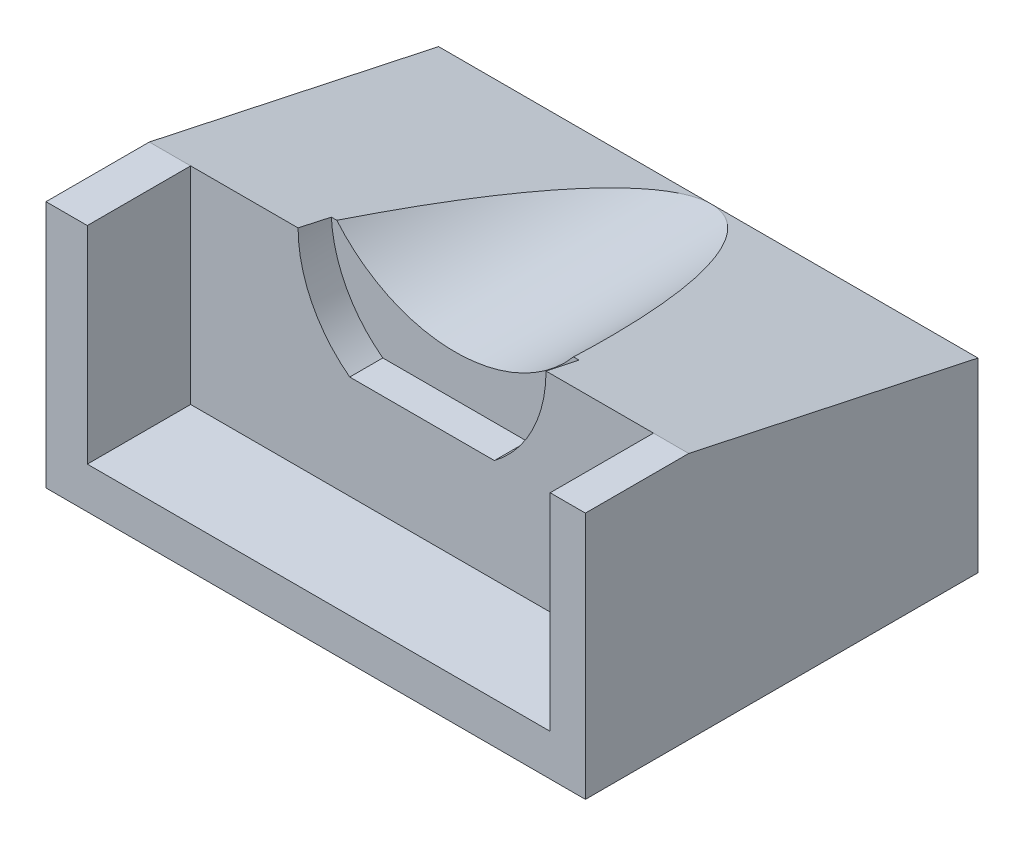
SolidWorks part; units mm, degrees
ref_plane "Front Plane" through (0, 0, 0) normal (0, 0, 1) x (1, 0, 0)
ref_plane "Top Plane" through (0, 0, 0) normal (0, 1, 0) x (1, 0, 0)
ref_plane "Right Plane" through (0, 0, 0) normal (1, 0, 0) x (0, 0, -1)
sketch "Sketch2" plane through (0, 0, 0) normal (0, 0, 1) x (1, 0, 0)
  line L1 (-11.2, 5) -> (11.2, 5)
  line L2 (-11.2, 5) -> (-11.2, -5)
  line L3 (-11.2, -5) -> (11.2, -5)
  line L4 (11.2, 5) -> (11.2, -5)
  line L5 (-11.2, 5) -> (11.2, -5) construction
  line L6 (-11.2, -5) -> (11.2, 5) construction
  point P0 (0, 0)
  dimension "D1" = 22.4
  dimension "D2" = 10
extrude "Boss-Extrude1" add sketch "Sketch2" along normal blind 14
sketch "Sketch3" plane through (0, 0, 14) normal (0, 0, 1) x (1, 0, 0)
  line L0 (-6, 5) -> (6, 5)
  line L1 (11.2, 5) -> (-11.2, 5) construction
  line L2 (-3.5, 0) -> (3.5, 0)
  line L3 (0, 5) -> (0, -5) construction
  line L4 (-11.2, -5) -> (11.2, -5) construction
  arc A0 (6, 5) -> (3.5, 0) centre (-0.25, 5) cw
  arc A1 (-6, 5) -> (-3.5, 0) centre (0.25, 5) ccw
  point P7 (0, 0)
  point P12 (4.1488, 0)
  point P13 (0, 0)
  point P14 (0, 0)
  point P15 (0, 0)
  point P19 (0, 0)
  dimension "D1" = 5
  dimension "D2" = 6
  dimension "D3" = 3.5
extrude "Cut-Extrude2" cut sketch "Sketch3" against normal blind 1.6
sketch "Sketch5" plane through (0, 0, 12.4) normal (0, 0, 1) x (1, 0, 0)
  line L0 (6, 5) -> (-6, 5) construction
  line L1 (-6, 5) -> (6, 5)
  arc A0 (-6, 5) -> (6, 5) centre (0, 9.5) ccw
  arc A1 (3.5, 0) -> (6, 5) centre (-0.25, 5) ccw construction
  point P3 (0, 2)
  point P10 (0, 5)
  dimension "D1" = 3
extrude "Cut-Extrude4" cut sketch "Sketch5" against normal through all
sketch "Sketch6" plane through (0, 0, 0) normal (0, 0, 1) x (1, 0, 0)
  line L0 (-11.2, 5) -> (-13.2, 5)
  line L1 (-13.2, 5) -> (-13.2, -7)
  line L2 (-13.2, -7) -> (12.9054, -7)
  line L3 (12.9054, -7) -> (12.9054, 5)
  line L4 (12.9054, 5) -> (11.2, 5)
  line L5 (11.2, 5) -> (11.2, -5)
  line L6 (11.2, -5) -> (-11.2, -5)
  line L7 (-11.2, -5) -> (-11.2, 5)
  dimension "D1" = 2
  dimension "D2" = 2
extrude "Boss-Extrude2" add sketch "Sketch6" along normal offset from surface (19 mm away) 5 up to face at (0, 1.1762, 14) offset beyond the face yes
sketch "Sketch7" plane through (-13.2, 0, 0) normal (-1, 0, 0) x (0, 0, 1)
  line L0 (0, 5) -> (14, 5)
  line L1 (19, 5) -> (0, 5) construction
  line L2 (14, 5) -> (0, 2)
  line L3 (0, 5) -> (0, -7) construction
  line L4 (0, 2) -> (0, 5)
  dimension "D1" = 3
  dimension "D2" = 14
extrude "Cut-Extrude5" cut sketch "Sketch7" against normal through all
